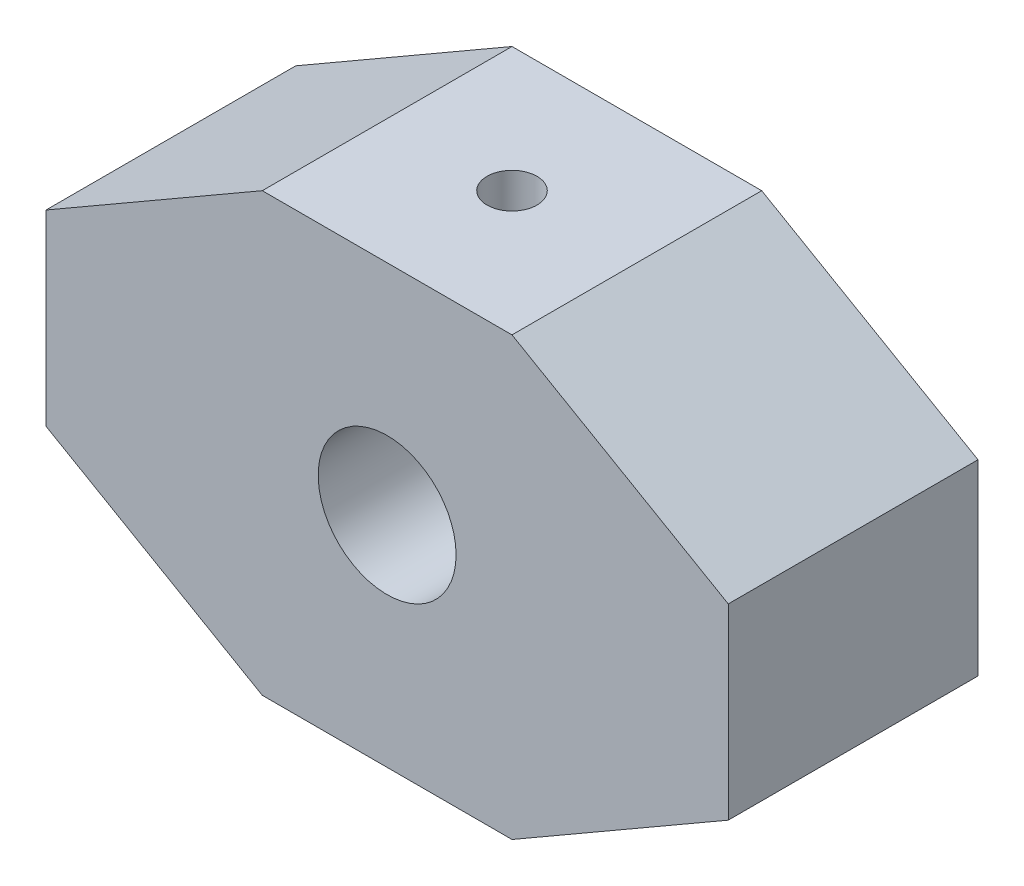
SolidWorks part; units mm, degrees
ref_plane "Plan de face" through (0, 0, 0) normal (0, 0, 1) x (1, 0, 0)
ref_plane "Plan de dessus" through (0, 0, 0) normal (0, 1, 0) x (1, 0, 0)
ref_plane "Plan de droite" through (0, 0, 0) normal (1, 0, 0) x (0, 0, -1)
sketch "Esquisse1" plane through (0, 0, 0) normal (0, 0, 1) x (1, 0, 0)
  line L0 (-0.3636, 1.7982) -> (-2.0957, 0.7982)
  line L1 (-2.0957, 0.7982) -> (-2.0957, -0.7018)
  line L2 (-2.0957, -0.7018) -> (-0.3636, -1.7018)
  line L3 (-0.3636, -1.7018) -> (1.6364, -1.7018)
  line L4 (1.6364, -1.7018) -> (3.3684, -0.7018)
  line L5 (3.3684, -0.7018) -> (3.3684, 0.7982)
  line L6 (3.3684, 0.7982) -> (1.6364, 1.7982)
  line L7 (1.6364, 1.7982) -> (-0.3636, 1.7982)
  dimension "D1" = 1.5
  dimension "D2" = 1.5
  dimension "D3" = 1
  dimension "D4" = 1
  dimension "D5" = 2
  dimension "D6" = 1
  dimension "D7" = 1
  dimension "D8" = 2
  dimension "D9" = 2
  dimension "D10" = 2
  dimension "D11" = 2
extrude "Boss.-Extru.1" add sketch "Esquisse1" along normal blind 2
sketch "Esquisse2" plane through (0, 0, 2) normal (0, 0, 1) x (1, 0, 0)
  line L0 (0.6364, 1.7982) -> (0.6364, -1.7018) construction
  line L1 (1.6364, 1.7982) -> (-0.3636, 1.7982) construction
  line L2 (-0.3636, -1.7018) -> (1.6364, -1.7018) construction
  line L3 (-2.0957, 0.0482) -> (3.3684, 0.0482) construction
  line L4 (-2.0957, 0.7982) -> (-2.0957, -0.7018) construction
  line L5 (3.3684, -0.7018) -> (3.3684, 0.7982) construction
  circle A0 centre (0.6363, 0.0482) radius 0.5522
  dimension "D1" = 1.1044
  dimension "D2" = 0.0001
  dimension "D3" = 0
extrude "Enlèv. mat.-Extru.1" cut sketch "Esquisse2" against normal blind 2
sketch "Esquisse3" plane through (0, 1.7982, 0) normal (0, 1, 0) x (1, 0, 0)
  line L0 (0.6364, 0) -> (0.6364, -2) construction
  line L1 (1.6364, 0) -> (-0.3636, 0) construction
  line L2 (1.6364, -2) -> (-0.3636, -2) construction
  line L3 (-0.3636, -1) -> (1.6364, -1) construction
  line L4 (-0.3636, -2) -> (-0.3636, 0) construction
  line L5 (1.6364, -2) -> (1.6364, 0) construction
  circle A0 centre (0.6364, -1) radius 0.2
  dimension "D3" = 0.4
  dimension "D1" = 0
  dimension "D2" = 0
extrude "Enlèv. mat.-Extru.2" cut sketch "Esquisse3" against normal blind 2
